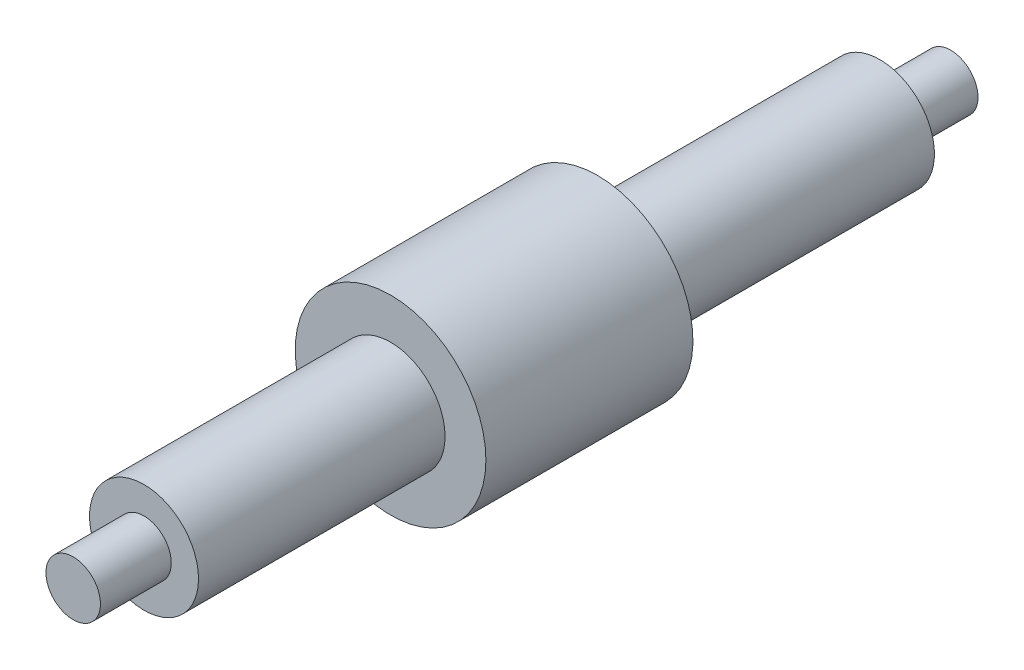
SolidWorks part; units mm, degrees
material "Сталь ШХ15 ГОСТ 801-78"
ref_plane "Plane1" through (0, 0, 0) normal (0, 0, 1) x (1, 0, 0)
ref_plane "Plane2" through (0, 0, 0) normal (0, 1, 0) x (1, 0, 0)
ref_plane "Plane3" through (0, 0, 0) normal (1, 0, 0) x (0, 0, -1)
sketch "Эскиз1" plane through (0, 0, 0) normal (0, 0, 1) x (1, 0, 0)
  circle A0 centre (0, 0) radius 2
  dimension "D1" = 4
extrude "Бобышка-Вытянуть1" add sketch "Эскиз1" against normal up to surface (27.0135 mm away) from surface contours A0
sketch "Эскиз2" plane through (0, 0, 31.8148) normal (0, 0, 1) x (1, 0, 0)
  circle A0 centre (0, 0) radius 1
  dimension "D1" = 2
extrude "Бобышка-Вытянуть2" add sketch "Эскиз2" along normal up to surface (2.6 mm away) contours A0
sketch "Эскиз4" plane through (0, 0, 4.8013) normal (0, 0, -1) x (-1, 0, 0)
  circle A0 centre (0, 0) radius 1
  dimension "D1" = 2
extrude "Бобышка-Вытянуть3" add sketch "Эскиз4" along normal up to surface (2.6 mm away)
sketch "Эскиз6" plane through (0, 0, 4.8013) normal (0, 0, -1) x (-1, 0, 0)
  circle A0 centre (0, 0) radius 3.5
  dimension "D1" = 7
extrude "Бобышка-Вытянуть5" add sketch "Эскиз6" along normal up to surface (7.6 mm away) from surface
